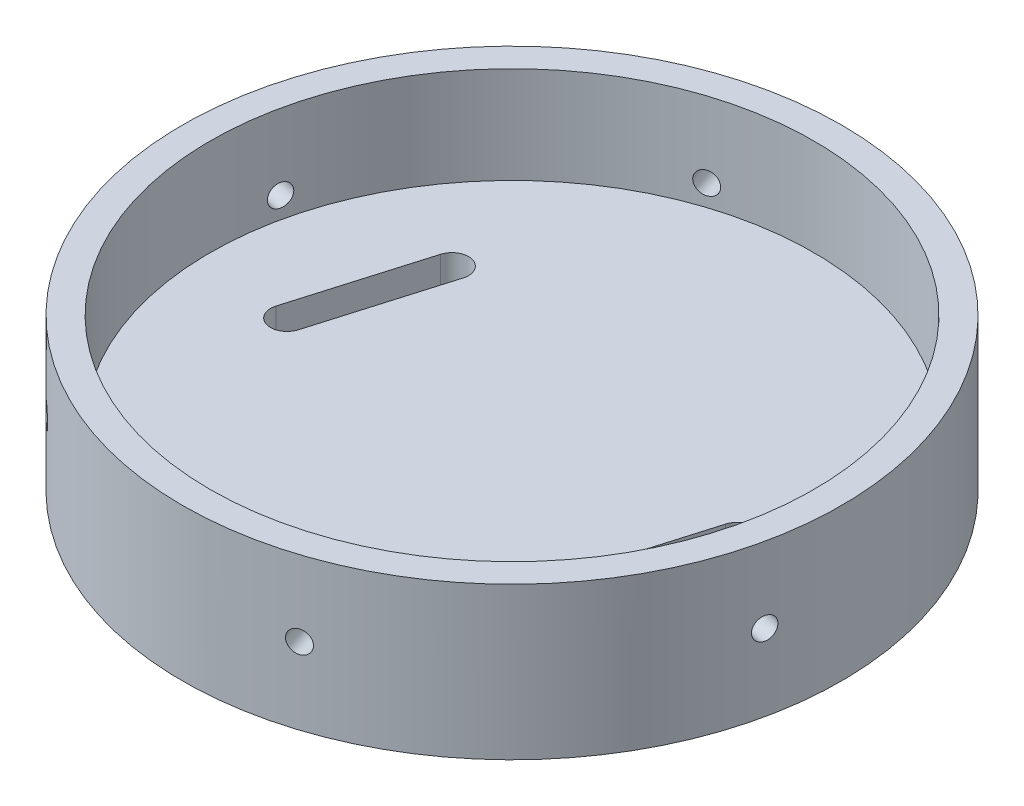
SolidWorks part; units mm, degrees
material "6061-T4 (SS)"
ref_plane "Front Plane" through (0, 0, 0) normal (0, 0, 1) x (1, 0, 0)
ref_plane "Top Plane" through (0, 0, 0) normal (0, 1, 0) x (1, 0, 0)
ref_plane "Right Plane" through (0, 0, 0) normal (1, 0, 0) x (0, 0, -1)
sketch "Sketch1" plane through (0, 0, 0) normal (0, 1, 0) x (1, 0, 0)
  circle A0 centre (0, 0) radius 75.692
  circle A1 centre (0, 0) radius 69.342
  dimension "D1" = 151.384
  dimension "D2" = 138.684
extrude "Boss-Extrude1" add sketch "Sketch1" along normal blind 22.225
sketch "Sketch2" plane through (0, 0, 0) normal (0, -1, 0) x (1, 0, 0)
  circle A0 centre (0, 0) radius 75.692
  dimension "D1" = 151.384
extrude "Boss-Extrude2" add sketch "Sketch2" along normal blind 12.7
hole_wizard "Tap Drill for 1/4-20 Tap1" positions "3DSketch2" profile "Sketch4" hole size "1/4-20" standard "ANSI Inch"
sketch3d "3DSketch2"
  line L0 (73.6526, 22.225, 17.4519) -> (73.9972, 4.8963, 15.9279)
  circle A1 centre (0, 22.225, 0) radius 75.692 construction
  point P0 (73.9972, 4.8963, 15.9279)
  point P10 (0, 97.917, 0)
  point P12 (-133.403, 50.4262, 0)
  dimension "D1" = 17.399
sketch "Sketch4" plane through (73.9972, 4.8963, 15.9279) normal (0, 1, 0) x (0.2104, 0, -0.9776)
  line L0 (0, 0) -> (0, 11.1858)
  line L1 (0, 11.1858) -> (2.5527, 9.652)
  line L2 (2.5527, 9.652) -> (2.5527, 0)
  line L5 (2.5527, 0) -> (0, 0)
  line L10 (0, 11.1858) -> (-2.5527, 9.652) construction
  line L11 (0, -6.35) -> (0, 107.95) construction
  dimension "Hole Dia." = 5.1054
  dimension "Hole Depth" = 9.652
  dimension "Drill Angle" = 118
pattern_circular "CirPattern1" count 6 over 360 about axis through (0, 22.225, 0) along (0, -1, 0) of "Tap Drill for 1/4-20 Tap1"
sketch "Sketch5" plane through (0, 0, 0) normal (0, 1, 0) x (1, 0, 0)
  circle A2 centre (0, 0) radius 44.45 construction
  point P0 (0, -50.8)
  point P1 (-43.1997, 10.4686)
  point P3 (43.1997, -10.4686)
  dimension "D2" = 88.9
  dimension "D1" = 50.8
  dimension "D3" = 88.9
hole_wizard "1/2 (0.5) Diameter Hole1" positions "Sketch6" profile "Sketch8" hole size "1/2" standard "ANSI Inch" end condition through all
sketch "Sketch6" plane through (0, 0, 0) normal (0, 1, 0) x (1, 0, 0)
  point P0 (0, -50.8)
sketch "Sketch8" plane through (0, 0, 50.8) normal (1, 0, 0) x (0, 0, 1)
  line L0 (0, 0) -> (0, 12.7)
  line L1 (0, 12.7) -> (6.35, 12.7)
  line L2 (6.35, 12.7) -> (6.35, 0)
  line L5 (6.35, 0) -> (0, 0)
  line L11 (0, -6.35) -> (0, 107.95) construction
  dimension "Thru Hole Dia." = 12.7
  dimension "Thru Hole Depth" = 12.7
sketch "Sketch11" plane through (0, 0, 0) normal (0, 1, 0) x (1, 0, 0)
  line L0 (-47.5107, -4.1489) -> (-38.8886, 25.0862) construction
  line L1 (-51.1651, -3.0712) -> (-42.543, 26.1639)
  line L2 (-43.8563, -5.2267) -> (-35.2343, 24.0084)
  line L3 (38.8886, -25.0862) -> (47.5107, 4.1489) construction
  line L4 (35.2343, -24.0084) -> (43.8563, 5.2267)
  line L5 (42.543, -26.1639) -> (51.1651, 3.0712)
  arc A0 (-51.1651, -3.0712) -> (-43.8563, -5.2267) centre (-47.5107, -4.1489) ccw
  arc A1 (-35.2343, 24.0084) -> (-42.543, 26.1639) centre (-38.8886, 25.0862) ccw
  arc A2 (35.2343, -24.0084) -> (42.543, -26.1639) centre (38.8886, -25.0862) ccw
  arc A3 (51.1651, 3.0712) -> (43.8563, 5.2267) centre (47.5107, 4.1489) ccw
  point P2 (-43.1997, 10.4686)
  point P9 (43.1997, -10.4686)
  dimension "D1" = 3.81
  dimension "D4" = 3.81
  dimension "D2" = 30.48
  dimension "D3" = 30.48
extrude "Cut-Extrude1" cut sketch "Sketch11" against normal through all
